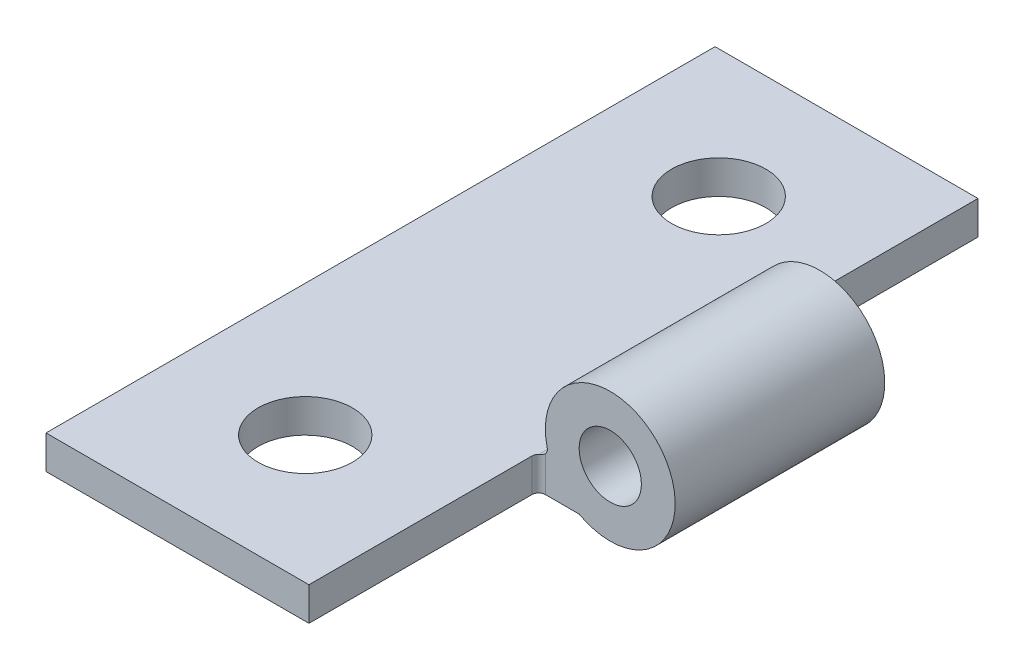
SolidWorks part; units mm, degrees
ref_plane "Front Plane" through (0, 0, 0) normal (0, 0, 1) x (1, 0, 0)
ref_plane "Top Plane" through (0, 0, 0) normal (0, 1, 0) x (1, 0, 0)
ref_plane "Right Plane" through (0, 0, 0) normal (1, 0, 0) x (0, 0, -1)
sketch "Sketch1" plane through (0, 0, 0) normal (0, 0, 1) x (1, 0, 0)
  line L4 (-2.4638, 4.7768) -> (-2.4638, 2.6146) construction
  line L5 (-2.4638, 2.6146) -> (-2.4638, -7.2406) construction
  line L6 (-17.6276, 2.6146) -> (-17.6276, 3.8846)
  line L7 (-17.6276, 3.8846) -> (-7.2242, 3.8846)
  line L8 (-17.6276, 2.6146) -> (-6.1087, 2.6146)
  circle A2 centre (-4.9276, 4.7768) radius 1.1811
  arc A3 (-6.1087, 2.6146) -> (-7.2242, 3.8846) centre (-4.9276, 4.7768) ccw
  point P11 (-12.7, 2.6146)
  point P17 (-12.7, 3.8846)
  point P18 (-2.4638, 4.7768)
extrude "Boss-Extrude1" add sketch "Sketch1" along normal blind 25.4
fillet "Fillet2" radius 0.254 1 edges at (-7.2242, 3.8846, 12.7)
sketch "Sketch2" plane through (0, 0, 0) normal (0, 0, -1) x (-1, 0, 0)
  circle A0 centre (4.9276, 4.7768) radius 2.4638
extrude "Cut-Extrude1" cut sketch "Sketch2" against normal blind 8.7211
sketch "Sketch3" plane through (0, 0, 25.4) normal (0, 0, 1) x (1, 0, 0)
  circle A0 centre (-4.9276, 4.7768) radius 2.4638
extrude "Cut-Extrude2" cut sketch "Sketch3" against normal blind 8.7211
sketch "Sketch5" plane through (0, 0, 0) normal (0, 0, -1) x (-1, 0, 0)
  line L0 (17.6276, 2.6146) -> (6.1087, 2.6146) construction
  line L1 (7.6454, 2.6146) -> (5.9181, 2.6146)
  line L2 (7.6454, 2.6146) -> (7.6454, 4.3784)
  line L3 (7.6454, 4.3784) -> (5.9181, 4.3784)
  line L4 (5.9181, 2.6146) -> (5.9181, 4.3784)
  line L5 (17.6276, 3.8846) -> (17.6276, 2.6146) construction
  dimension "D1" = 9.9822
extrude "Cut-Extrude3" cut sketch "Sketch5" against normal blind 8.7211
sketch "Sketch6" plane through (0, 0, 25.4) normal (0, 0, 1) x (1, 0, 0)
  line L0 (-17.6276, 2.6146) -> (-6.1087, 2.6146) construction
  line L1 (-7.6454, 2.6146) -> (-5.6808, 2.6146)
  line L2 (-7.6454, 2.6146) -> (-7.6454, 4.5077)
  line L3 (-7.6454, 4.5077) -> (-5.6808, 4.5077)
  line L4 (-5.6808, 2.6146) -> (-5.6808, 4.5077)
  line L5 (-17.6276, 3.8846) -> (-17.6276, 2.6146) construction
  dimension "D1" = 9.9822
extrude "Cut-Extrude4" cut sketch "Sketch6" against normal blind 8.7211
fillet "Fillet3" radius 0.254 1 edges at (-7.6454, 3.2496, 16.6789)
fillet "Fillet4" radius 0.254 1 edges at (-7.6454, 3.2496, 8.7211)
sketch "Sketch7" plane through (0, 3.8846, 0) normal (0, 1, 0) x (1, 0, 0)
  line L0 (-7.6454, 0) -> (-17.6276, 0) construction
  line L1 (-17.6276, -25.4) -> (-17.6276, 0) construction
  line L2 (-7.6454, -25.4) -> (-17.6276, -25.4) construction
  circle A0 centre (-12.6365, -4.8514) radius 1.7907
  circle A1 centre (-12.6365, -20.5486) radius 1.7907
  dimension "D1" = 3.5814
  dimension "D4" = 3.5814
  dimension "D2" = 4.8514
  dimension "D3" = 4.9911
  dimension "D5" = 4.8514
extrude "Cut-Extrude5" cut sketch "Sketch7" against normal blind 2.54
ref_plane "Plane1" through (-20.1676, 0, 0) normal (-1, 0, 0) x (0, 0, 1)
